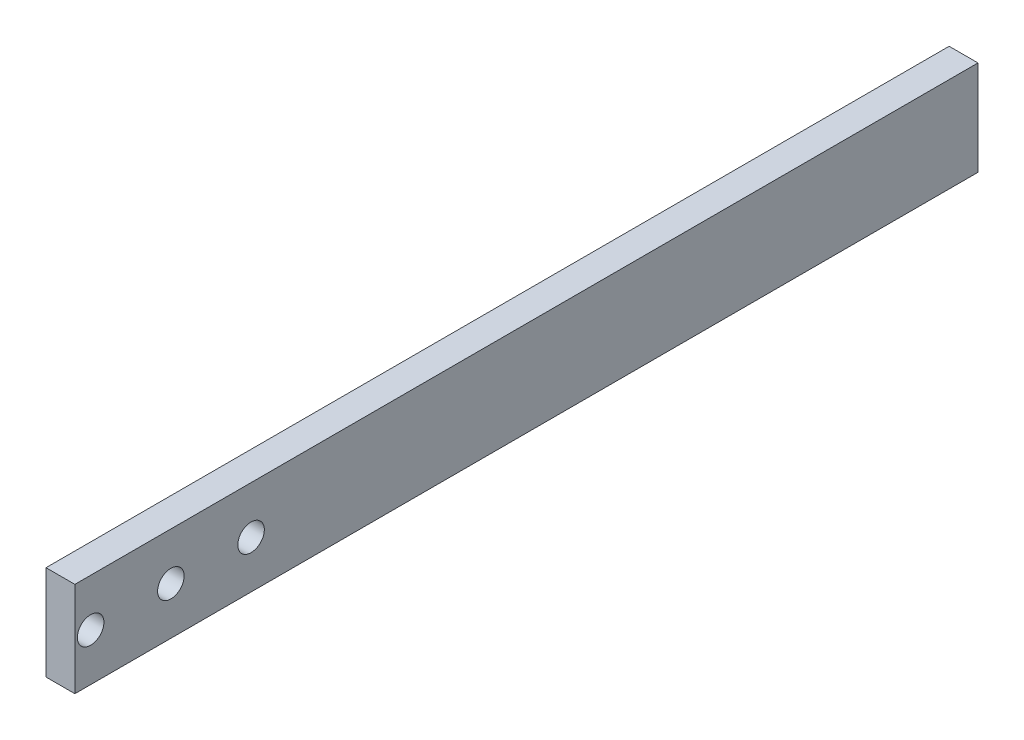
SolidWorks part; units mm, degrees
ref_plane "Front Plane" through (0, 0, 0) normal (0, 0, 1) x (1, 0, 0)
ref_plane "Top Plane" through (0, 0, 0) normal (0, 1, 0) x (1, 0, 0)
ref_plane "Right Plane" through (0, 0, 0) normal (1, 0, 0) x (0, 0, -1)
sketch "Sketch1" plane through (0, 0, 0) normal (0, 1, 0) x (1, 0, 0)
  line L15 (-45.43, 268) -> (-45.43, 125)
  line L17 (-50, 268) -> (-50, 125)
  line L18 (-45.43, 125) -> (-50, 125)
  line L19 (-50, 268) -> (-45.43, 268)
  dimension "D1" = 143
  dimension "D9" = 4.57
extrude "Boss-Extrude1" add sketch "Sketch1" along normal blind 18
sketch "Sketch2" plane through (-50, 0, 0) normal (-1, 0, 0) x (0, 0, 1)
  line L0 (-268, 18) -> (-125, 18) construction
  line L1 (-125, 18) -> (-125, 0) construction
  circle A0 centre (-127.5, 10.5) radius 2.1
  circle A1 centre (-140.2, 10.5) radius 2.1
  circle A2 centre (-152.9, 10.5) radius 2.1
  dimension "D3" = 4.2
  dimension "D4" = 7.5
  dimension "D5" = 2.5
  dimension "D1" = 12.7
  dimension "D2" = 12.7
extrude "Cut-Extrude1" cut sketch "Sketch2" against normal blind 18
sketch "Sketch3" plane through (-50, 0, 0) normal (-1, 0, 0) x (0, 0, 1)
  line L1 (-125, 0) -> (-270, 0)
  line L2 (-125, 0) -> (-125, 3)
  line L3 (-125, 3) -> (-270, 3)
  line L4 (-270, 0) -> (-270, 3)
  dimension "D1" = 145
  dimension "D2" = 3
extrude "Cut-Extrude2" cut sketch "Sketch3" against normal blind 10
